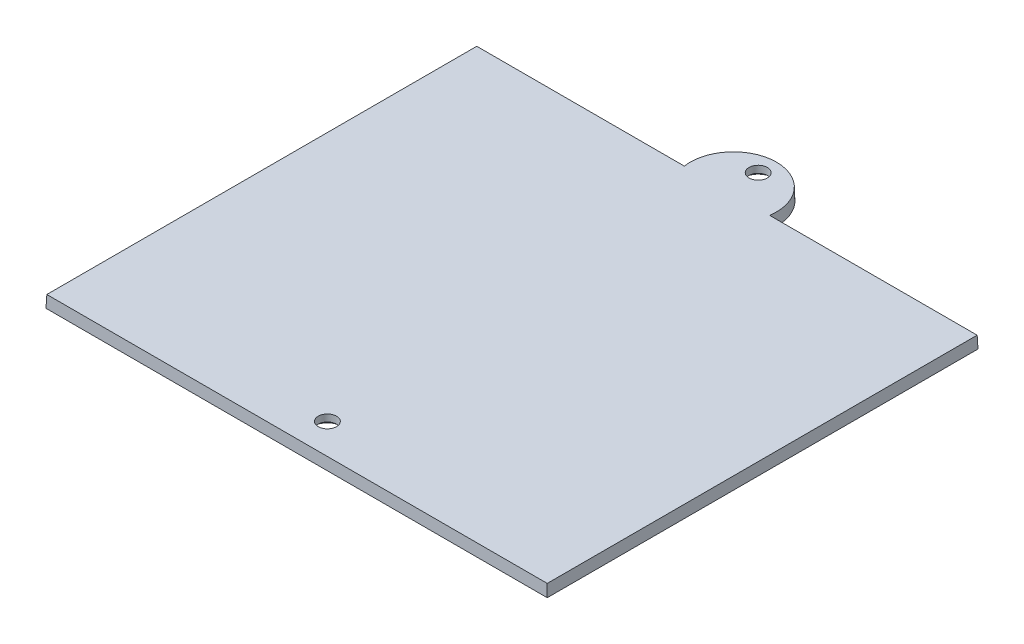
SolidWorks part; units mm, degrees
ref_plane "Front Plane" through (0, 0, 0) normal (0, 0, 1) x (1, 0, 0)
ref_plane "Top Plane" through (0, 0, 0) normal (0, 1, 0) x (1, 0, 0)
ref_plane "Right Plane" through (0, 0, 0) normal (1, 0, 0) x (0, 0, -1)
ref_plane "Plane1" through (0, 56.6839, 0) normal (0, -1, 0) x (-1, 0, 0)
sketch "Sketch1" plane through (0, 56.6839, 0) normal (0, -1, 0) x (-1, 0, 0)
  line L0 (-95.0337, -185.908) -> (-95.0337, -112.1701) construction
  line L1 (-9.5589, -185.908) -> (-95.0337, -185.908) construction
  line L2 (-9.5589, -112.1701) -> (-9.5589, -185.908) construction
  line L3 (-95.0337, -112.1701) -> (-60.5463, -112.1701) construction
  line L4 (-44.0463, -112.1701) -> (-9.5589, -112.1701) construction
  line L5 (-95.0337, -185.908) -> (-95.0337, -112.1701) construction
  line L6 (-9.5589, -185.908) -> (-95.0337, -185.908) construction
  line L7 (-9.5589, -112.1701) -> (-9.5589, -185.908) construction
  line L8 (-95.0337, -112.1701) -> (-60.5463, -112.1701) construction
  line L9 (-44.0463, -112.1701) -> (-9.5589, -112.1701) construction
  line L10 (-45.1156, -113.1701) -> (-10.5589, -113.1701)
  line L11 (-94.0337, -113.1701) -> (-59.477, -113.1701)
  line L12 (-94.0337, -113.1701) -> (-94.0337, -184.908)
  line L13 (-94.0337, -184.908) -> (-10.5589, -184.908)
  line L14 (-10.5589, -113.1701) -> (-10.5589, -184.908)
  circle A0 centre (-52.2963, -179.783) radius 1.5 construction
  circle A1 centre (-52.2963, -108.0451) radius 1.5 construction
  arc A2 (-44.0463, -112.1701) -> (-60.5463, -112.1701) centre (-52.2963, -112.1701) ccw construction
  circle A3 centre (-52.2963, -179.783) radius 1.5 construction
  circle A4 centre (-52.2963, -108.0451) radius 1.5 construction
  arc A5 (-44.0463, -112.1701) -> (-60.5463, -112.1701) centre (-52.2963, -112.1701) ccw construction
  arc A6 (-45.1156, -113.1701) -> (-59.477, -113.1701) centre (-52.2963, -112.1701) ccw
  point P13 (-52.2963, -179.783)
  point P15 (-52.2963, -108.0451)
  dimension "D5" = 1
  dimension "D1" = 1
  dimension "D2" = 1
  dimension "D3" = 1
  dimension "D4" = 1
extrude "Boss-Extrude1" add sketch "Sketch1" against normal blind 2 draft 2
hole_wizard "CSK for #3 Flat Head Machine Screw (100)1" positions "3DSketch1" profile "Sketch3" countersink size "#3" standard "ANSI Inch" end condition through all
sketch3d "3DSketch1"
  point P0 (52.2963, 56.6839, 108.0451)
  point P3 (52.2963, 56.6839, 179.783)
sketch "Sketch3" plane through (52.2963, 56.6839, 108.0451) normal (1, 0, 0) x (0, 0, -1)
  line L0 (0, 0) -> (0, 2)
  line L1 (0, 2) -> (1.524, 2)
  line L2 (1.524, 2) -> (1.524, 0.8419)
  line L3 (1.524, 0.8419) -> (2.5273, 0)
  line L5 (2.5273, 0) -> (0, 0)
  line L6 (-1.524, 0.8419) -> (-2.5273, 0) construction
  line L11 (0, -6.35) -> (0, 107.95) construction
  dimension "Thru Hole Dia." = 3.048
  dimension "Thru Hole Depth" = 2
  dimension "Near C'Sink Dia." = 5.0546
  dimension "Near C'Sink Angle" = 100
